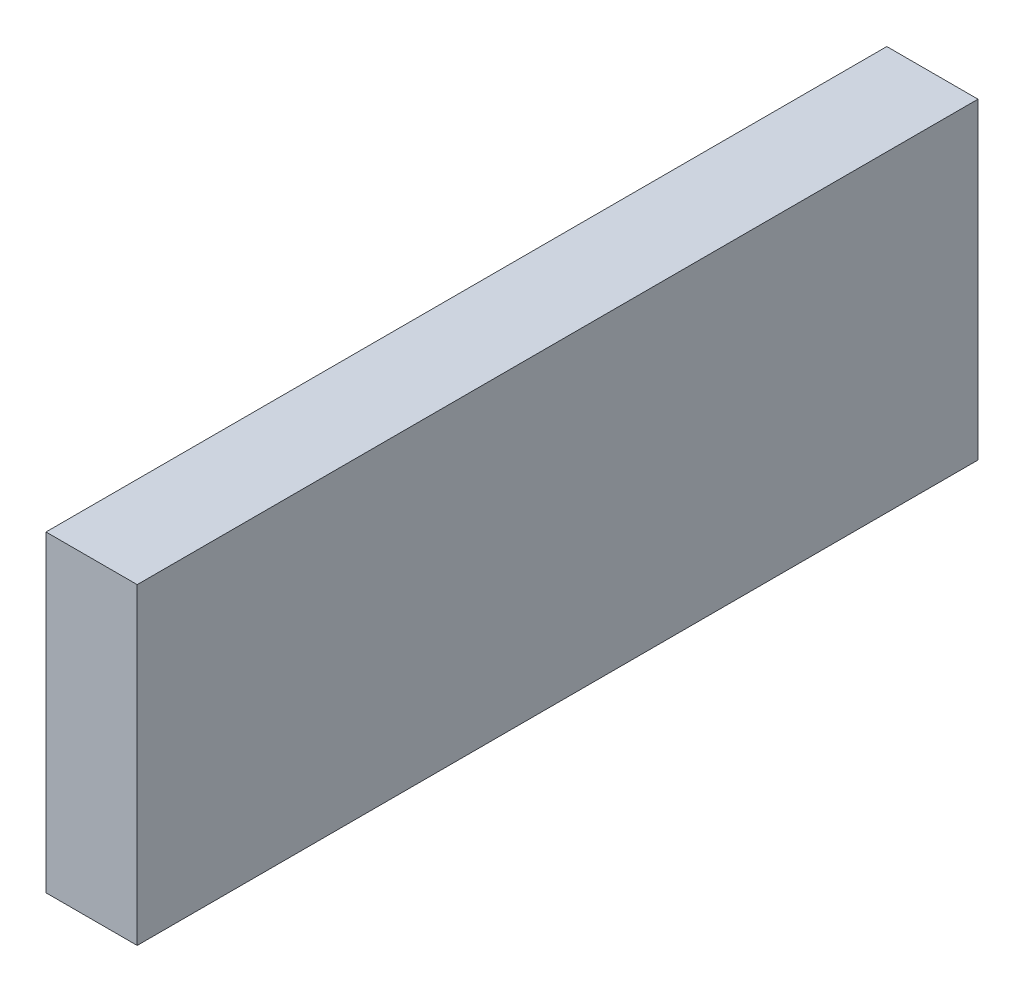
SolidWorks part; units mm, degrees
ref_plane "Alzado" through (0, 0, 0) normal (0, 0, 1) x (1, 0, 0)
ref_plane "Planta" through (0, 0, 0) normal (0, 1, 0) x (1, 0, 0)
ref_plane "Vista lateral" through (0, 0, 0) normal (1, 0, 0) x (0, 0, -1)
sketch "Croquis1" plane through (0, 0, 0) normal (1, 0, 0) x (0, 0, -1)
  line L1 (0, 0) -> (46.1005, 0)
  line L2 (0, 0) -> (0, 17.1347)
  line L3 (0, 17.1347) -> (46.1005, 17.1347)
  line L4 (46.1005, 0) -> (46.1005, 17.1347)
extrude "Saliente-Extruir1" add sketch "Croquis1" along normal blind 5
shell "Vaciado2" thickness 0.5
